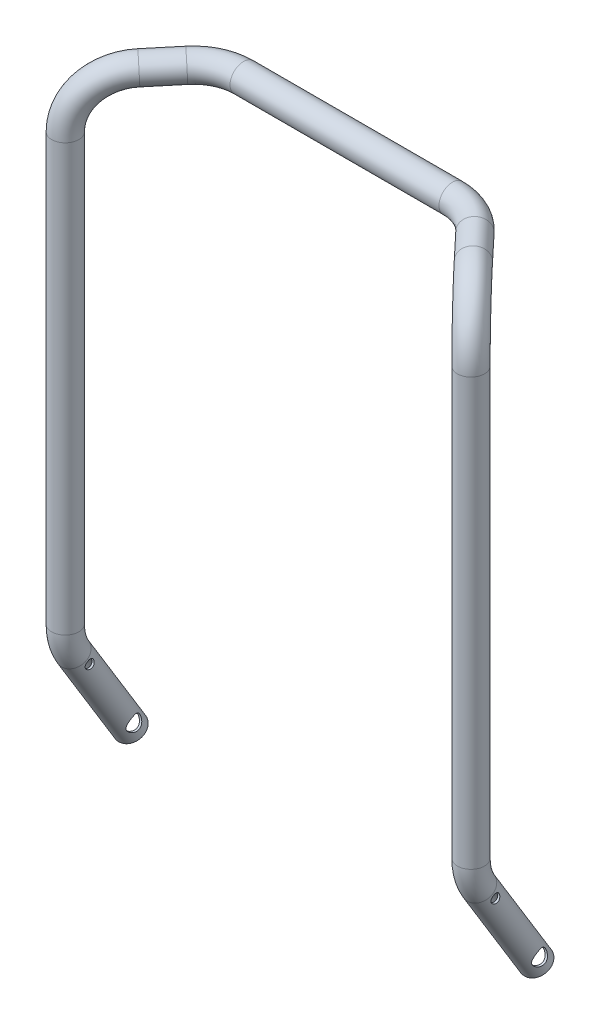
SolidWorks part; units mm, degrees
ref_plane "Спереди" through (0, 0, 0) normal (0, 0, 1) x (1, 0, 0)
ref_plane "Сверху" through (0, 0, 0) normal (0, 1, 0) x (1, 0, 0)
ref_plane "Справа" through (0, 0, 0) normal (1, 0, 0) x (0, 0, -1)
sketch3d "Трехмерный эскиз1"
  line L0 (0, 14.0774, 0) -> (0, 407.0029, 0)
  line L1 (32.774, 456.9611, -35.0106) -> (54.1441, 458.2398, -57.839)
  line L2 (90.6728, 459.1267, -73.6726) -> (186.9661, 459.1267, -73.6726)
  line L3 (0, -12.0095, -7.3447) -> (0, -98.1071, -60)
  arc A0 (0, 407.0029, 0) -> (32.774, 456.9611, -35.0106) centre (34.1702, 407.0029, -36.502) ccw
  arc A1 (54.1441, 458.2398, -57.839) -> (90.6728, 459.1267, -73.6726) centre (90.6728, 456.3304, -23.7508) ccw
  arc A2 (0, -12.0095, -7.3447) -> (0, 14.0774, 0) centre (0, 14.0774, -50) ccw
  point P8 (0, 455, 0)
  point P9 (-2.3319, 407.0029, -70.6722)
  point P12 (68.9661, 459.1267, -73.6726)
  point P13 (90.6728, 406.4086, -26.5472)
  point P16 (0, 0, 0)
  point P17 (-50, 14.0774, -50)
  dimension "D1" = 455
  dimension "D8" = 50
  dimension "D9" = 50
  dimension "D10" = 50
  dimension "D2" = 115
  dimension "D3" = 465
  dimension "D4" = 201
  dimension "D5" = 60
  dimension "D6" = 118
  dimension "D7" = 101
ref_plane "Плоскость1" through (0, -98.1071, -60) normal (0, -0.8531, -0.5217) x (-1, 0, 0)
sketch "Эскиз3" plane through (0, -98.1071, -60) normal (0, -0.8531, -0.5217) x (-1, 0, 0)
  circle A0 centre (0, 0) radius 12.5
  circle A1 centre (0, 0) radius 10.5
sweep "По траектории3" add profiles "Эскиз3" path "Трехмерный эскиз1"
ref_plane "Плоскость2" through (186.9661, 0, 0) normal (1, 0, 0) x (0, 0, -1)
mirror "Зеркальное отражение3" about plane through (186.9661, 459.1267, -73.6726) normal (-1, 0, 0) of bodies 106
sketch "Эскиз4" plane through (186.9661, 0, 0) normal (1, 0, 0) x (0, 0, -1)
  line L6 (70.6638, -91.5853) -> (18.0086, -5.4878) construction
  line L7 (70.6638, -91.5853) -> (18.0086, -5.4878) construction
  line L8 (12.6463, -127.0675) -> (107.3537, -69.1467) construction
  circle A2 centre (10.4348, -17.0621) radius 4.1
  circle A3 centre (52.1739, -85.3105) radius 7.05
  dimension "D1" = 12.5
  dimension "D3" = 14.1
  dimension "D4" = 8.2
  dimension "D2" = 12.5
  dimension "D5" = 15
  dimension "D6" = 80
extrude "Вырез-Вытянуть1" cut sketch "Эскиз4" against normal through all and the other way through all
